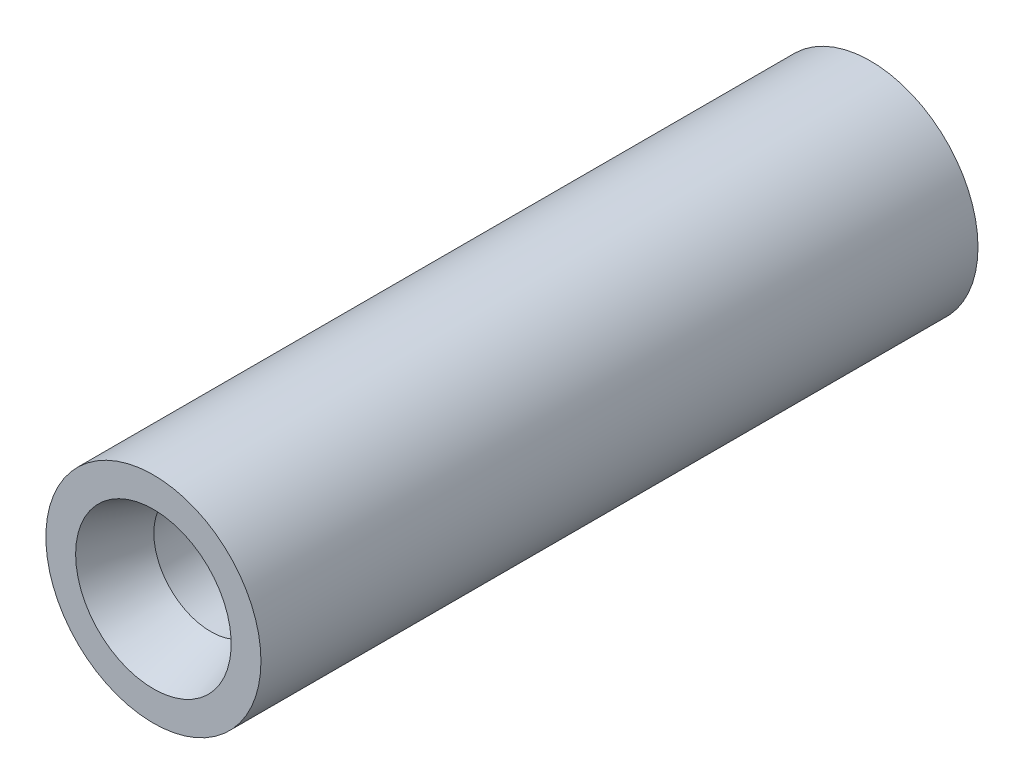
SolidWorks part; units mm, degrees
ref_plane "Ebene1" through (0, 0, 0) normal (0, 0, 1) x (1, 0, 0)
ref_plane "Ebene2" through (0, 0, 0) normal (0, 1, 0) x (1, 0, 0)
ref_plane "Ebene3" through (0, 0, 0) normal (1, 0, 0) x (0, 0, -1)
sketch "Skizze1" plane through (0, 0, 0) normal (0, 0, 1) x (1, 0, 0)
  circle A0 centre (0, 0) radius 15
  dimension "D1" = 30
extrude "Aufsatz-Linear austragen1" add sketch "Skizze1" along normal blind 100
sketch "Skizze3" plane through (0, 0, 0) normal (1, 0, 0) x (0, 0, -1)
  line L0 (0, 0) -> (-100, 0) construction
  line L1 (-100, 15) -> (-100, -15) construction
  line L2 (-100, 0) -> (-100, 10.8493)
  line L3 (-100, 10.8493) -> (-92, 7.9375)
  line L4 (-92, 7.9375) -> (-72, 7.9375)
  line L5 (-72, 7.9375) -> (-66.7463, 0)
  line L6 (-100, 0) -> (-66.7463, 0)
  dimension "D1" = 56.5
  dimension "D2" = 15.875
  dimension "D3" = 20
  dimension "D4" = 8
  dimension "D5" = 20
revolve "Schnitt-Rotation1" cut sketch "Skizze3" angle 360 about L0
cosmetic thread "Gewindedarstellung1" parameters "D1"=5, "D2"=20
